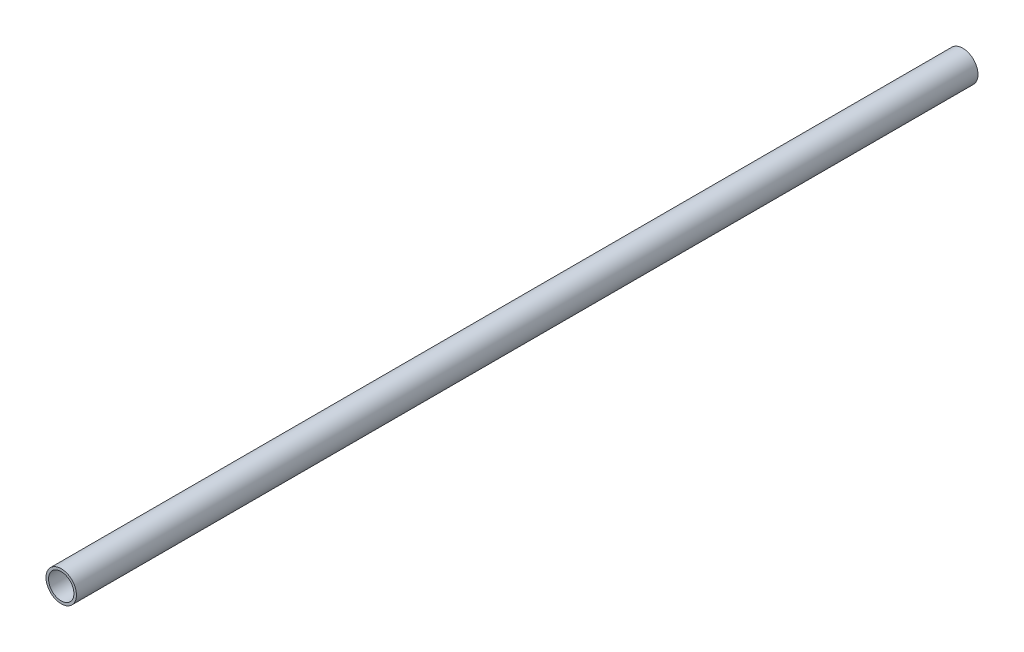
SolidWorks part; units mm, degrees
ref_plane "Спереди" through (0, 0, 0) normal (0, 0, 1) x (1, 0, 0)
ref_plane "Сверху" through (0, 0, 0) normal (0, 1, 0) x (1, 0, 0)
ref_plane "Справа" through (0, 0, 0) normal (1, 0, 0) x (0, 0, -1)
sketch "Эскиз1" plane through (0, 0, 0) normal (0, 0, 1) x (1, 0, 0)
  circle A0 centre (0, 0) radius 24
  dimension "D1" = 48
extrude "Бобышка-Вытянуть1" add sketch "Эскиз1" along normal blind 1420
sketch "Эскиз2" plane through (0, 0, 0) normal (0, 0, -1) x (-1, 0, 0)
  circle A0 centre (0, 0) radius 20
  dimension "D1" = 40
extrude "Вырез-Вытянуть1" cut sketch "Эскиз2" against normal through all
